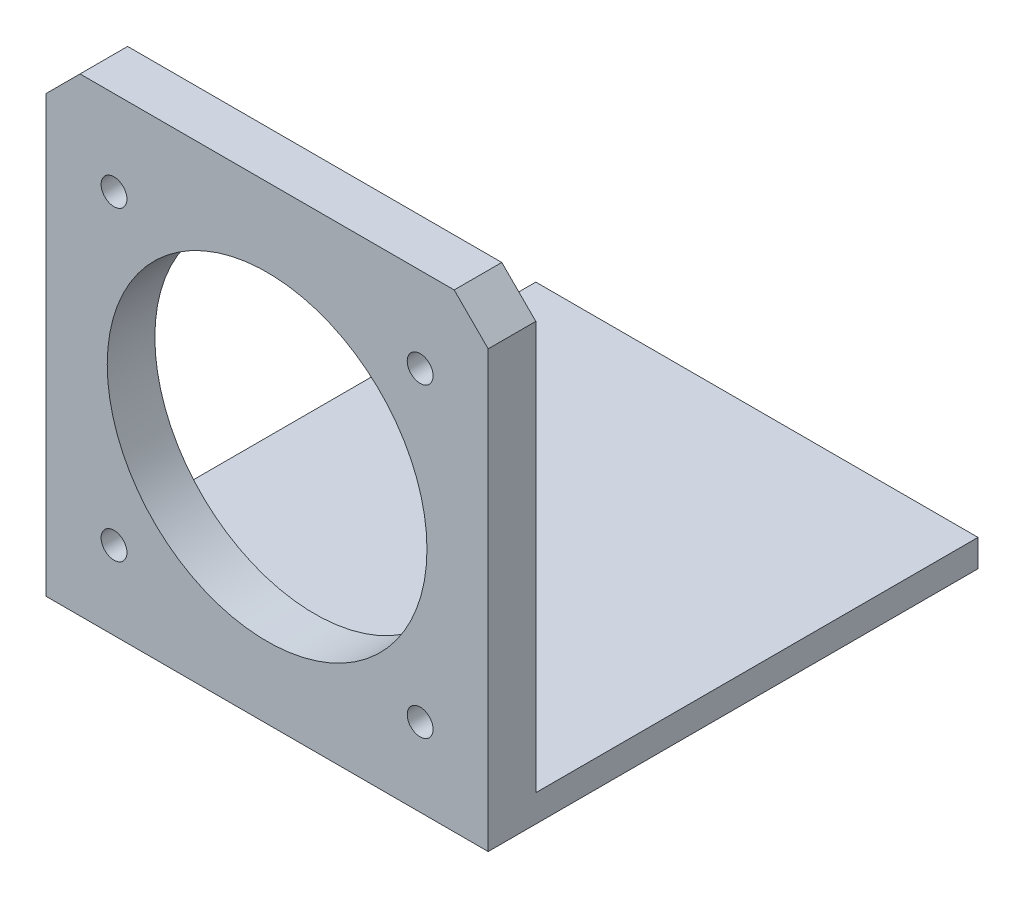
SolidWorks part; units mm, degrees
ref_plane "Front Plane" through (0, 0, 0) normal (0, 0, 1) x (1, 0, 0)
ref_plane "Top Plane" through (0, 0, 0) normal (0, 1, 0) x (1, 0, 0)
ref_plane "Right Plane" through (0, 0, 0) normal (1, 0, 0) x (0, 0, -1)
sketch "Sketch2" plane through (0, 0, 0) normal (1, 0, 0) x (0, 0, -1)
  line L2 (0, 0) -> (0, 65)
  line L3 (0, 65) -> (-7, 65)
  line L4 (-7, -4) -> (-7, 65)
  line L5 (0, 0) -> (65, 0)
  line L7 (-7, -4) -> (65, -4)
  line L8 (65, 0) -> (65, -4)
  dimension "D1" = 65
  dimension "D2" = 7
  dimension "D3" = 4
  dimension "D4" = 65
extrude "Boss-Extrude1" add sketch "Sketch2" along normal blind 65 contours L2 L3 L4 L7 L8 L5
chamfer "Chamfer1" distance 5 angle 45 2 edges at (65, 65, 3.5) (0, 65, 3.5)
sketch "Sketch4" plane through (0, 0, 7) normal (0, 0, 1) x (1, 0, 0)
  line L1 (60, 65) -> (5, 65) construction
  line L2 (32.5, 30) -> (32.5, 45.8311) construction
  line L3 (5, 2.5) -> (60, 2.5) construction
  line L4 (5, 2.5) -> (5, 57.5) construction
  line L5 (5, 57.5) -> (60, 57.5) construction
  line L6 (60, 2.5) -> (60, 57.5) construction
  line L7 (5, 2.5) -> (60, 57.5) construction
  line L8 (5, 57.5) -> (60, 2.5) construction
  line L9 (32.5, 30) -> (41.9451, 30) construction
  circle A0 centre (32.5, 30) radius 23.5
  circle A1 centre (10, 52.5) radius 1.9
  circle A2 centre (55, 52.5) radius 1.9
  circle A3 centre (55, 7.5) radius 1.9
  circle A4 centre (10, 7.5) radius 1.9
  point P7 (32.5, 65)
  dimension "D1" = 47
  dimension "D3" = 55
  dimension "D5" = 3.8
  dimension "D2" = 30
  dimension "D4" = 55
  dimension "D6" = 5
  dimension "D7" = 5
extrude "Cut-Extrude1" cut sketch "Sketch4" against normal blind 65
